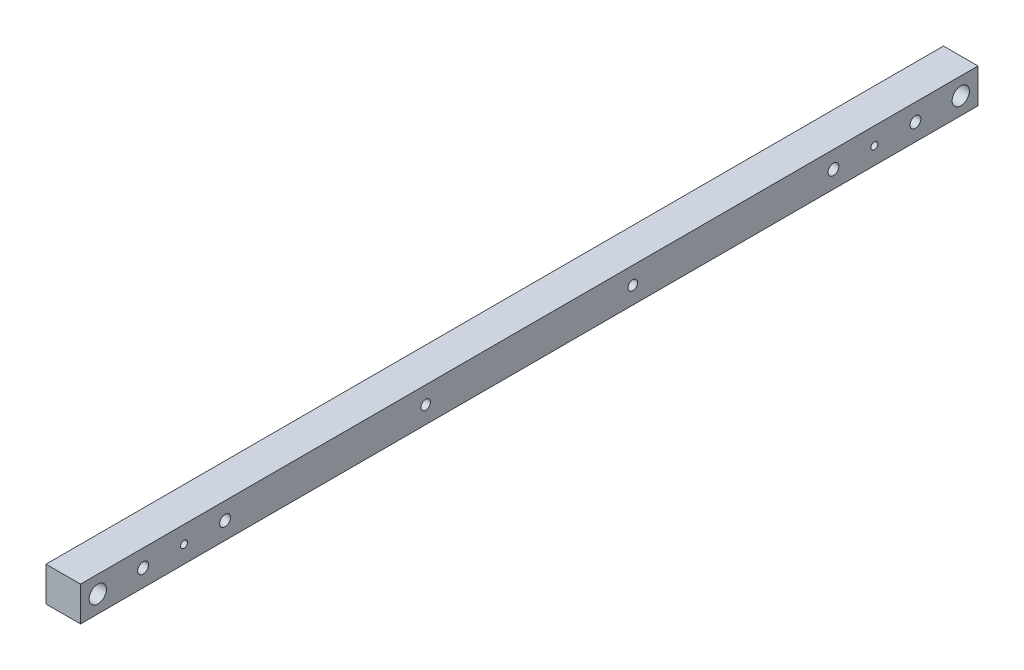
SolidWorks part; units mm, degrees
ref_plane "Front Plane" through (0, 0, 0) normal (0, 0, 1) x (1, 0, 0)
ref_plane "Top Plane" through (0, 0, 0) normal (0, 1, 0) x (1, 0, 0)
ref_plane "Right Plane" through (0, 0, 0) normal (1, 0, 0) x (0, 0, -1)
sketch "Sketch1" plane through (0, 0, 0) normal (0, 0, 1) x (1, 0, 0)
  line L5 (-12.7, -12.7) -> (12.7, -12.7)
  line L6 (-12.7, -12.7) -> (-12.7, 12.7)
  line L7 (-12.7, 12.7) -> (12.7, 12.7)
  line L8 (12.7, -12.7) -> (12.7, 12.7)
  line L9 (-12.7, -12.7) -> (12.7, 12.7) construction
  line L10 (-12.7, 12.7) -> (12.7, -12.7) construction
  point P0 (0, 0)
  dimension "D1" = 25.4
  dimension "D2" = 25.4
extrude "Boss-Extrude1" add sketch "Sketch1" along normal blind 660.4
sketch "Sketch2" plane through (-12.7, 0, 0) normal (1, 0, 0) x (0, 0, -1)
  line L0 (0, 0) -> (-660.4, 0) construction
  line L1 (-660.4, 12.7) -> (-660.4, -12.7) construction
  line L2 (-330.2, 0) -> (-330.2, 46.4779) construction
  line L4 (0, -12.7) -> (0, 12.7) construction
  circle A0 centre (-12.7, 0) radius 6.35
  circle A1 centre (-647.7, 0) radius 6.35
  dimension "D1" = 12.7
  dimension "D2" = 12.7
extrude "Cut-Extrude4" cut sketch "Sketch2" against normal through all and the other way through all contours A1 | A0
sketch "Sketch3" plane through (-12.7, 0, 0) normal (-1, 0, 0) x (0, 0, 1)
  line L1 (660.4, 12.7) -> (0, 12.7) construction
  line L2 (330.2, 12.7) -> (330.2, 76.0207) construction
  line L3 (660.4, 12.7) -> (660.4, -12.7) construction
  circle A0 centre (554.0375, 0) radius 3.97
  circle A1 centre (106.3625, 0) radius 3.97
  circle A2 centre (614.3625, 0) radius 3.97
  circle A3 centre (584.2, 0) radius 2.55
  circle A4 centre (46.0375, 0) radius 3.97
  circle A5 centre (76.2, 0) radius 2.55
  point P18 (0, 0)
  dimension "D1" = 7.94
  dimension "D2" = 76.2
  dimension "D4" = 7.94
  dimension "D5" = 60.325
  dimension "D6" = 5.1
  dimension "D7" = 30.1625
  dimension "D3" = 12.7
extrude "Cut-Extrude5" cut sketch "Sketch3" against normal through all
sketch "Sketch10" plane through (-12.7, 0, 0) normal (-1, 0, 0) x (0, 0, 1)
  line L0 (330.2, 12.7) -> (330.2, 75.2381) construction
  line L1 (660.4, 12.7) -> (0, 12.7) construction
  circle A0 centre (406.4, 0) radius 3.5
  circle A1 centre (254, 0) radius 3.5
  dimension "D1" = 7
  dimension "D3" = 76.2
  dimension "D2" = 12.7
extrude "Cut-Extrude6" cut sketch "Sketch10" against normal through all
